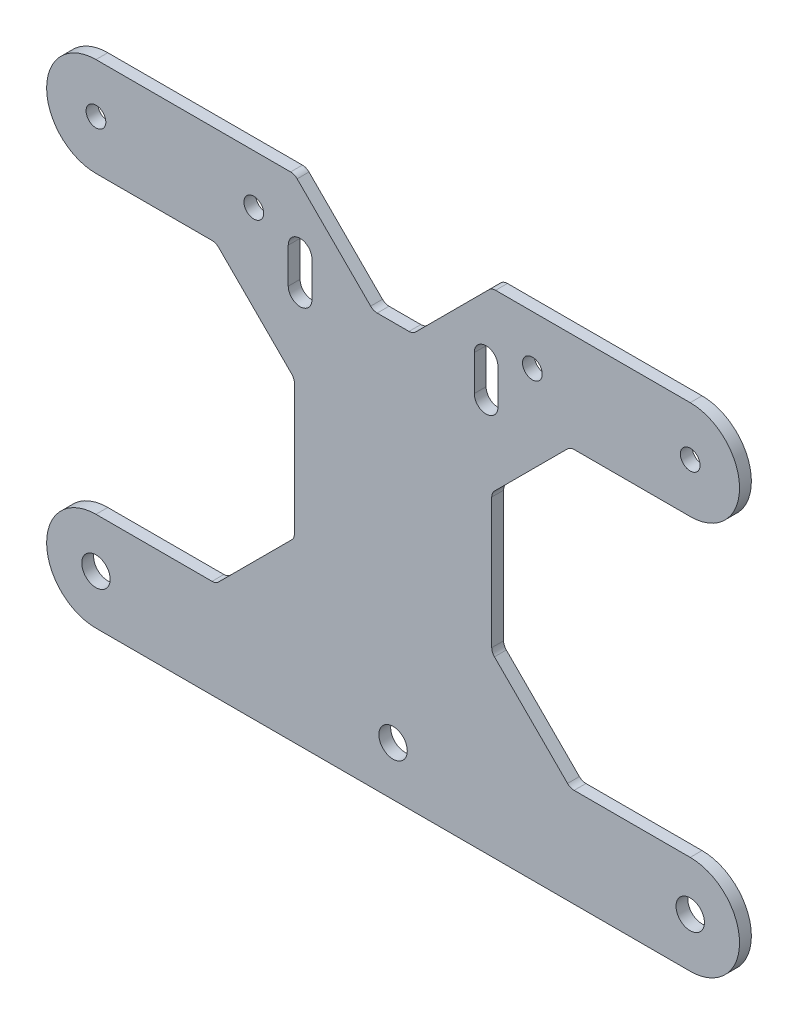
SolidWorks part; units mm, degrees
ref_plane "Front" through (0, 0, 0) normal (0, 0, 1) x (1, 0, 0)
ref_plane "Top" through (0, 0, 0) normal (0, 1, 0) x (1, 0, 0)
ref_plane "Right" through (0, 0, 0) normal (1, 0, 0) x (0, 0, -1)
sketch "Model" plane through (0, 0, 0) normal (0, 0, 1) x (1, 0, 0)
  line L0 (-75.3, 0) -> (75.3, 0)
  line L1 (75.3, 25) -> (45.8734, 25)
  line L2 (-75.3, 25) -> (-45.8734, 25)
  line L3 (23.57, 99.43) -> (23.57, 108.43) construction
  line L4 (-25, 45.8734) -> (-25, 78.9266)
  line L5 (26.57, 99.43) -> (26.57, 108.43)
  line L6 (44.2117, 25.6883) -> (25.6883, 44.2117)
  line L7 (-44.2117, 25.6883) -> (-25.6883, 44.2117)
  line L8 (-25.6883, 80.5883) -> (-44.2117, 99.1117)
  line L9 (25, 45.8734) -> (25, 78.9266)
  line L10 (25.6883, 80.5883) -> (44.2117, 99.1117)
  line L11 (20.57, 99.43) -> (20.57, 108.43)
  line L12 (75.3, 99.8) -> (45.8734, 99.8)
  line L14 (-24.3117, 124.1117) -> (-5.6883, 105.4883)
  line L15 (25.9734, 124.8) -> (75.3, 124.8)
  line L16 (-75.3, 99.8) -> (-45.8734, 99.8)
  line L17 (-4.0266, 104.8) -> (4.0266, 104.8)
  line L18 (24.3117, 124.1117) -> (5.6883, 105.4883)
  line L19 (-25.9734, 124.8) -> (-75.3, 124.8)
  line L20 (0, 0) -> (0, 104.8) construction
  line L21 (-75.3, 112.3) -> (-75.3, 12.5) construction
  line L22 (-75.3, 12.5) -> (75.3, 12.5) construction
  line L23 (-75.3, 112.3) -> (-35.3, 112.3) construction
  line L24 (-23.57, 99.43) -> (-23.57, 108.43) construction
  line L25 (-26.57, 99.43) -> (-26.57, 108.43)
  line L26 (-20.57, 99.43) -> (-20.57, 108.43)
  arc A0 (-75.3, 124.8) -> (-75.3, 99.8) centre (-75.3, 112.3) ccw
  arc A1 (-75.3, 25) -> (-75.3, 0) centre (-75.3, 12.5) ccw
  circle A2 centre (75.3, 12.5) radius 3.6
  arc A3 (75.3, 25) -> (75.3, 0) centre (75.3, 12.5) cw
  circle A4 centre (0, 12.5) radius 3.6
  arc A5 (45.8734, 25) -> (44.2117, 25.6883) centre (45.8734, 27.35) cw
  circle A6 centre (-75.3, 12.5) radius 3.6
  arc A7 (26.57, 99.43) -> (20.57, 99.43) centre (23.57, 99.43) cw
  arc A8 (20.57, 108.43) -> (26.57, 108.43) centre (23.57, 108.43) cw
  circle A11 centre (-35.3, 112.3) radius 2.5
  arc A12 (25.6883, 44.2117) -> (25, 45.8734) centre (27.35, 45.8734) cw
  arc A13 (25, 78.9266) -> (25.6883, 80.5883) centre (27.35, 78.9266) cw
  circle A14 centre (-75.3, 112.3) radius 2.5
  arc A15 (-5.6883, 105.4883) -> (-4.0266, 104.8) centre (-4.0266, 107.15) ccw
  arc A16 (44.2117, 99.1117) -> (45.8734, 99.8) centre (45.8734, 97.45) cw
  circle A17 centre (35.3, 112.3) radius 2.5
  circle A18 centre (75.3, 112.3) radius 2.5
  arc A19 (75.3, 124.8) -> (75.3, 99.8) centre (75.3, 112.3) cw
  arc A20 (24.3117, 124.1117) -> (25.9734, 124.8) centre (25.9734, 122.45) cw
  arc A21 (-45.8734, 25) -> (-44.2117, 25.6883) centre (-45.8734, 27.35) ccw
  arc A22 (-25.6883, 44.2117) -> (-25, 45.8734) centre (-27.35, 45.8734) ccw
  arc A23 (-25, 78.9266) -> (-25.6883, 80.5883) centre (-27.35, 78.9266) ccw
  arc A24 (-44.2117, 99.1117) -> (-45.8734, 99.8) centre (-45.8734, 97.45) ccw
  arc A25 (-24.3117, 124.1117) -> (-25.9734, 124.8) centre (-25.9734, 122.45) ccw
  arc A26 (5.6883, 105.4883) -> (4.0266, 104.8) centre (4.0266, 107.15) cw
  arc A27 (-26.57, 99.43) -> (-20.57, 99.43) centre (-23.57, 99.43) ccw
  arc A28 (-20.57, 108.43) -> (-26.57, 108.43) centre (-23.57, 108.43) ccw
  point P20 (23.57, 103.93)
  point P36 (-23.57, 103.93)
  dimension "D1" = 7.2
  dimension "D2" = 5
  dimension "D3" = 124.8
  dimension "D4" = 12.5
  dimension "D5" = 2.35
  dimension "D6" = 175.6
  dimension "D14" = 3
  dimension "D9" = 62.8
  dimension "D7" = 40
  dimension "D8" = 135
  dimension "D10" = 135
  dimension "D11" = 26.196
  dimension "D12" = 8.0532
  dimension "D13" = 20
  dimension "D15" = 9
  dimension "D16" = 16.37
  dimension "D17" = 23.57
extrude "Boss-Extrude1" add sketch "Model" along normal blind 3
